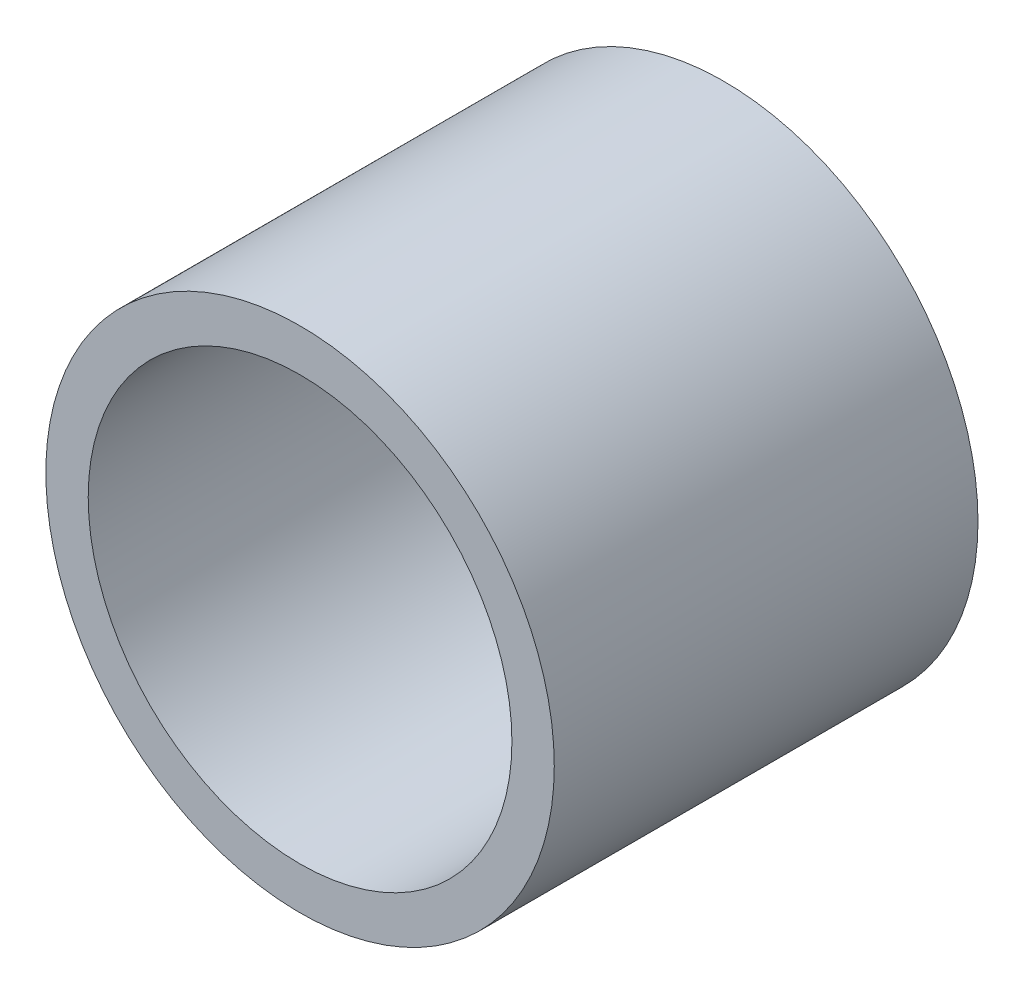
SolidWorks part; units mm, degrees
ref_plane "Front Plane" through (0, 0, 0) normal (0, 0, 1) x (1, 0, 0)
ref_plane "Top Plane" through (0, 0, 0) normal (0, 1, 0) x (1, 0, 0)
ref_plane "Right Plane" through (0, 0, 0) normal (1, 0, 0) x (0, 0, -1)
sketch "Sketch1" plane through (0, 0, 0) normal (0, 0, 1) x (1, 0, 0)
  circle A0 centre (0, 0) radius 15
  dimension "D1" = 30
extrude "Extrude-Thin1" add sketch "Sketch1" along normal mid plane 30 thin
sketch "Sketch2" plane through (0, 0, 0) normal (0, 0, 1) x (1, 0, 0)
  circle A0 centre (0, 0) radius 5
  dimension "D1" = 10
extrude "Boss-Extrude1" add sketch "Sketch2" against normal blind 10 separate body
sketch "Sketch5" plane through (0, 0, 0) normal (0, 0, 1) x (1, 0, 0)
  line L0 (-14.3103, 0.0102) -> (-13.9805, 0.6499) construction
  line L1 (0, -1) -> (-5.3, -1)
  line L2 (0, -1) -> (0, 1)
  line L3 (0, 1) -> (-5.3, 1)
  line L4 (-5.3, -1) -> (-5.3, -0.7826)
  line L5 (-16.3, -1) -> (-14.3, -1)
  line L6 (-16.3, -1) -> (-16.3, 1)
  line L7 (-16.3, 1) -> (-14.3, 1)
  line L8 (-14.3, -1) -> (-14.3, -0.7336)
  line L9 (-13.6238, 0.6477) -> (-12.9789, -0.6422) construction
  line L10 (-12.6211, -0.6422) -> (-11.9789, 0.6422) construction
  line L11 (-11.6211, 0.6422) -> (-10.9789, -0.6422) construction
  line L12 (-10.6211, -0.6422) -> (-9.9789, 0.6422) construction
  line L13 (-9.6211, 0.6422) -> (-8.9789, -0.6422) construction
  line L14 (-8.6211, -0.6422) -> (-7.9789, 0.6422) construction
  line L15 (-7.6211, 0.6422) -> (-6.9789, -0.6422) construction
  line L16 (-16.3, 0) -> (0, 0) construction
  line L17 (-6.6211, -0.6422) -> (-5.9789, 0.6422) construction
  line L18 (-13.8, 1) -> (-5.8, 1) construction
  line L19 (-12.8, -1) -> (-6.8, -1) construction
  line L20 (-5.6211, 0.6422) -> (-5.3, 0) construction
  line L21 (-13.9805, 0.6499) -> (-13.8, 1) construction
  line L22 (-13.8, 1) -> (-13.6238, 0.6477) construction
  line L23 (-12.9789, -0.6422) -> (-12.8, -1) construction
  line L24 (-12.8, -1) -> (-12.6211, -0.6422) construction
  line L25 (-11.9789, 0.6422) -> (-11.8, 1) construction
  line L26 (-11.8, 1) -> (-11.6211, 0.6422) construction
  line L27 (-10.9789, -0.6422) -> (-10.8, -1) construction
  line L28 (-10.8, -1) -> (-10.6211, -0.6422) construction
  line L29 (-8.9789, -0.6422) -> (-8.8, -1) construction
  line L30 (-8.8, -1) -> (-8.6211, -0.6422) construction
  line L31 (-6.9789, -0.6422) -> (-6.8, -1) construction
  line L32 (-6.8, -1) -> (-6.6211, -0.6422) construction
  line L33 (-9.9789, 0.6422) -> (-9.8, 1) construction
  line L34 (-9.8, 1) -> (-9.6211, 0.6422) construction
  line L35 (-7.9789, 0.6422) -> (-7.8, 1) construction
  line L36 (-7.8, 1) -> (-7.6211, 0.6422) construction
  line L37 (-14.3, -0.7336) -> (-13.9193, 0.0047)
  line L38 (-5.8, 1) -> (-5.9789, 0.6422) construction
  line L39 (-5.8, 1) -> (-5.6211, 0.6422) construction
  line L40 (-13.693, 0.0033) -> (-13.2919, -0.7988)
  line L41 (-12.3081, -0.7988) -> (-11.9118, -0.0062)
  line L42 (-11.6882, -0.0062) -> (-11.2919, -0.7988)
  line L43 (-10.3081, -0.7988) -> (-9.9118, -0.0062)
  line L44 (-9.6882, -0.0062) -> (-9.2919, -0.7988)
  line L45 (-8.3081, -0.7988) -> (-7.9118, -0.0062)
  line L46 (-7.6882, -0.0062) -> (-7.2919, -0.7988)
  line L47 (-6.3081, -0.7988) -> (-5.9118, -0.0062)
  line L48 (-5.6882, -0.0062) -> (-5.3, -0.7826)
  line L49 (-14.3, 0.794) -> (-14.2916, 0.8103)
  line L50 (-13.3108, 0.8042) -> (-12.9118, 0.0062)
  line L51 (-12.6882, 0.0062) -> (-12.2919, 0.7988)
  line L52 (-11.3081, 0.7988) -> (-10.9118, 0.0062)
  line L53 (-10.6882, 0.0062) -> (-10.2919, 0.7988)
  line L54 (-9.3081, 0.7988) -> (-8.9118, 0.0062)
  line L55 (-8.6882, 0.0062) -> (-8.2919, 0.7988)
  line L56 (-7.3081, 0.7988) -> (-6.8972, -0.0229)
  line L57 (-6.7028, -0.0229) -> (-6.2919, 0.7988)
  line L58 (-5.3081, 0.7988) -> (-5.3, 0.7826)
  line L59 (-14.6214, 0.1706) -> (-14.2916, 0.8103) construction
  line L60 (-13.9992, -0.1502) -> (-13.8048, 0.2269) construction
  line L61 (-5.3081, 0.7988) -> (-4.987, 0.1565) construction
  line L62 (-5.8, 0.2174) -> (-5.613, -0.1565) construction
  line L63 (-14.3, 0.794) -> (-14.3, 1)
  line L64 (-14.3, 0.794) -> (-14.3, -0.7336) construction
  line L65 (-13.8048, 0.2269) -> (-13.2919, -0.7988) construction
  line L66 (-13.3108, 0.8042) -> (-12.8, -0.2174) construction
  line L67 (-12.8, -0.2174) -> (-12.2919, 0.7988) construction
  line L68 (-11.8, 0.2174) -> (-11.2919, -0.7988) construction
  line L69 (-12.3081, -0.7988) -> (-11.8, 0.2174) construction
  line L70 (-11.3081, 0.7988) -> (-10.8, -0.2174) construction
  line L71 (-10.8, -0.2174) -> (-10.2919, 0.7988) construction
  line L72 (-10.3081, -0.7988) -> (-9.8, 0.2174) construction
  line L73 (-9.8, 0.2174) -> (-9.2919, -0.7988) construction
  line L74 (-9.3081, 0.7988) -> (-8.8, -0.2174) construction
  line L75 (-8.8, -0.2174) -> (-8.2919, 0.7988) construction
  line L76 (-8.3081, -0.7988) -> (-7.8, 0.2174) construction
  line L77 (-7.8, 0.2174) -> (-7.2919, -0.7988) construction
  line L78 (-6.8, -0.2174) -> (-6.2919, 0.7988) construction
  line L79 (-7.3081, 0.7988) -> (-6.8, -0.2174) construction
  line L80 (-6.3081, -0.7988) -> (-5.8, 0.2174) construction
  line L81 (-5.3, 0.7826) -> (-5.3, 1)
  line L82 (-5.3, 0.7826) -> (-5.3, -0.7826) construction
  arc A0 (-13.9805, 0.6499) -> (-13.6238, 0.6477) centre (-13.8027, 0.5582) cw construction
  arc A1 (-11.9789, 0.6422) -> (-11.6211, 0.6422) centre (-11.8, 0.5528) cw construction
  arc A2 (-12.9789, -0.6422) -> (-12.6211, -0.6422) centre (-12.8, -0.5528) ccw construction
  arc A3 (-10.9789, -0.6422) -> (-10.6211, -0.6422) centre (-10.8, -0.5528) ccw construction
  arc A4 (-9.9789, 0.6422) -> (-9.6211, 0.6422) centre (-9.8, 0.5528) cw construction
  arc A5 (-7.9789, 0.6422) -> (-7.6211, 0.6422) centre (-7.8, 0.5528) cw construction
  arc A6 (-8.9789, -0.6422) -> (-8.6211, -0.6422) centre (-8.8, -0.5528) ccw construction
  arc A7 (-6.9789, -0.6422) -> (-6.6211, -0.6422) centre (-6.8, -0.5528) ccw construction
  arc A8 (-5.9789, 0.6422) -> (-5.6211, 0.6422) centre (-5.8, 0.5528) cw construction
  arc A9 (-13.8048, 0.2269) -> (-13.8048, 0.2269) centre (-13.8048, 0.2269) cw
  arc A10 (-13.2919, -0.7988) -> (-12.3081, -0.7988) centre (-12.8, -0.5528) ccw
  arc A11 (-11.8, 0.2174) -> (-11.8, 0.2174) centre (-11.8, 0.2174) cw
  arc A12 (-11.2919, -0.7988) -> (-10.3081, -0.7988) centre (-10.8, -0.5528) ccw
  arc A13 (-9.8, 0.2174) -> (-9.8, 0.2174) centre (-9.8, 0.2174) cw
  arc A14 (-9.2919, -0.7988) -> (-8.3081, -0.7988) centre (-8.8, -0.5528) ccw
  arc A15 (-7.8, 0.2174) -> (-7.8, 0.2174) centre (-7.8, 0.2174) cw
  arc A16 (-7.2919, -0.7988) -> (-6.3081, -0.7988) centre (-6.8, -0.5528) ccw
  arc A17 (-5.8, 0.2174) -> (-5.8, 0.2174) centre (-5.8, 0.2174) cw
  arc A18 (-14.2916, 0.8103) -> (-13.3108, 0.8042) centre (-13.8027, 0.5582) cw
  arc A19 (-12.8, -0.2174) -> (-12.8, -0.2174) centre (-12.8, -0.2174) ccw
  arc A20 (-12.2919, 0.7988) -> (-11.3081, 0.7988) centre (-11.8, 0.5528) cw
  arc A21 (-10.8, -0.2174) -> (-10.8, -0.2174) centre (-10.8, -0.2174) ccw
  arc A22 (-10.2919, 0.7988) -> (-9.3081, 0.7988) centre (-9.8, 0.5528) cw
  arc A23 (-8.8, -0.2174) -> (-8.8, -0.2174) centre (-8.8, -0.2174) ccw
  arc A24 (-8.2919, 0.7988) -> (-7.3081, 0.7988) centre (-7.8, 0.5528) cw
  arc A25 (-6.8, -0.2174) -> (-6.8, -0.2174) centre (-6.8, -0.2174) ccw
  arc A26 (-6.2919, 0.7988) -> (-5.3081, 0.7988) centre (-5.8, 0.5528) cw
  arc A28 (-13.693, 0.0033) -> (-13.9193, 0.0047) centre (-13.8048, 0.2269) ccw
  arc A29 (-12.9118, 0.0062) -> (-12.6882, 0.0062) centre (-12.8, -0.2174) ccw
  arc A30 (-11.6882, -0.0062) -> (-11.9118, -0.0062) centre (-11.8, 0.2174) ccw
  arc A31 (-10.9118, 0.0062) -> (-10.6882, 0.0062) centre (-10.8, -0.2174) ccw
  arc A32 (-9.6882, -0.0062) -> (-9.9118, -0.0062) centre (-9.8, 0.2174) ccw
  arc A33 (-8.9118, 0.0062) -> (-8.6882, 0.0062) centre (-8.8, -0.2174) ccw
  arc A34 (-7.6882, -0.0062) -> (-7.9118, -0.0062) centre (-7.8, 0.2174) ccw
  arc A35 (-6.8972, -0.0229) -> (-6.7028, -0.0229) centre (-6.8, -0.2174) ccw
  arc A36 (-5.6882, -0.0062) -> (-5.9118, -0.0062) centre (-5.8, 0.2174) ccw
  point P10 (0, 0)
  point P21 (-10.3, 0)
  dimension "D14" = 0.2
  dimension "D15" = 0.2
  dimension "D16" = 0.2
  dimension "D17" = 0.2
  dimension "D18" = 0.2
  dimension "D19" = 0.2
  dimension "D20" = 0.2
  dimension "D21" = 0.2
  dimension "D22" = 0.2
  dimension "D24" = 0.2664
  dimension "D25" = 0.5
  dimension "D26" = 0.5
  dimension "D27" = 0.5
  dimension "D28" = 0.5
  dimension "D29" = 0.5
  dimension "D30" = 0.5
  dimension "D31" = 0.5
  dimension "D32" = 0.5
  dimension "D1" = 5.3
  dimension "D2" = 9
  dimension "D3" = 2
  dimension "D4" = 1
  dimension "D5" = 1
  dimension "D6" = 1
  dimension "D7" = 2
  dimension "D8" = 1
  dimension "D9" = 2
  dimension "D10" = 0.5
  dimension "D11" = 1
  dimension "D12" = 0.35
  dimension "D13" = 2
  dimension "D23" = 0.35
